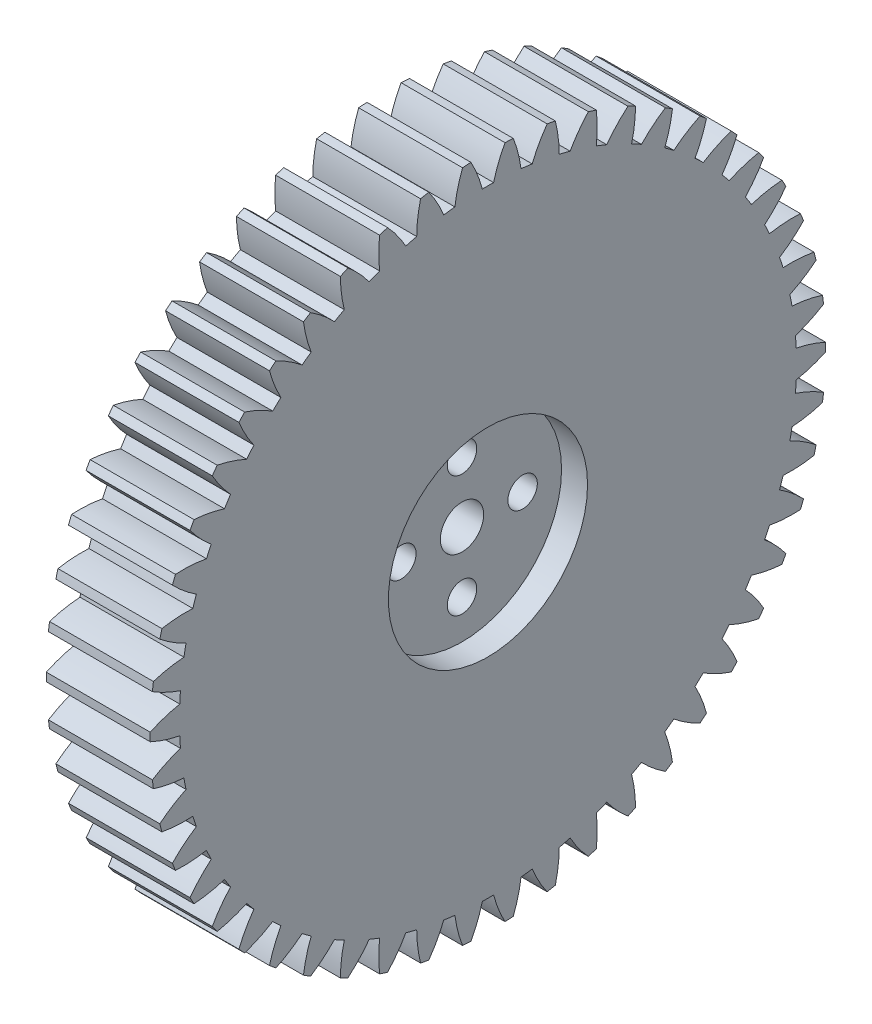
SolidWorks part; units mm, degrees
ref_plane "Plane1" through (0, 0, 0) normal (0, 0, 1) x (1, 0, 0)
ref_plane "Plane2" through (0, 0, 0) normal (0, 1, 0) x (1, 0, 0)
ref_plane "Plane3" through (0, 0, 0) normal (1, 0, 0) x (0, 0, -1)
sketch "HoldingSke" plane through (0, 0, 0) normal (0, 1, 0) x (1, 0, 0)
  line L0 (0, 0) -> (0.4285, -0.5107)
  line L1 (-15, 0) -> (100, 0) construction
  line L2 (0, 0) -> (-2.1039, 2.3779)
  line L3 (0, 0) -> (-11.863, 4.5341)
  line L4 (0, 0) -> (5.5511, 6.6156)
  line L5 (0, 0) -> (-46.8476, -17.4728)
  line L6 (0, 0) -> (-9.9476, -6.7116)
  line L7 (-2.1039, 2.3779) -> (8.6586, 51.2059)
  line L8 (-76.2, 54.61) -> (-74.8, 54.61)
  line L9 (-71.009, 38.7566) -> (-53.1078, 45.2721)
  line L10 (-76.2, 71.12) -> (104.1128, 71.12)
  line L11 (0, 0) -> (-12, 0)
  line L12 (-76.2, 101.6) -> (-76.147, 101.6)
  line L13 (24.9733, 27.94) -> (52.9518, 28.4284)
  line L14 (24.9733, 27.94) -> (24.9743, 27.94)
  line L15 (24.9733, 27.94) -> (100.4006, 29.5858)
  line L16 (-63.627, -1.5) -> (-12.827, -1.5)
  circle A0 centre (0, 0) radius 4
  circle A1 centre (0, 0) radius 35.624
  circle A2 centre (0, 0) radius 37.5
  circle A3 centre (0, 0) radius 4
  dimension "MHD" = 71.248
  dimension "Hub_dia" = 75
  dimension "Bore" = 8
  dimension "MBD" = 8
  dimension "Num_teeth" = 50
  dimension "Pitch" = 0.6667
  dimension "Overall_len" = 50
  dimension "Show_teeth" = 50
  dimension "Thickness" = 12
  dimension "OAL" = 50.0001
  dimension "T_dim" = 1.4
  dimension "Ap" = 20
  dimension "H" = 19.05
  dimension "Pitch_radius" = 180.3128
  dimension "Width" = 12
  dimension "Backlash" = 0.053
  dimension "Addendum_fac" = 1
  dimension "Dedendum_fac" = 1.25
  dimension "Clearance_fac" = 0.25
  dimension "Dedendum_add" = 0.001
  dimension "Module" = 1.5
sketch "BasProSke" plane through (0, 0, 0) normal (0, 1, 0) x (1, 0, 0)
  line L0 (-10, 0) -> (60, 0) construction
  line L1 (0, 0) -> (0, 39)
  line L2 (0, 0) -> (12, 0)
  line L3 (12, 0) -> (12, 39)
  line L4 (12, 39) -> (0, 39)
  dimension "Thickness" = 12
  dimension "Diameter" = 78
revolve "Base-Revolve" add sketch "BasProSke" angle 360 about L0
sketch "TooCutSke" plane through (0, 0, 0) normal (1, 0, 0) x (0, 0, -1)
  line L1 (0, 0) -> (0, 107) construction
  line L2 (0, 0) -> (-1.2706, 37.4785) construction
  line L3 (0, 0) -> (-4.7073, 74.8207) construction
  line L4 (-1.2706, 37.4785) -> (-2.3537, 37.4103) construction
  arc A0 (0.65, 35.6181) -> (-0.65, 35.6181) centre (0, 0) ccw
  arc A1 (1.9801, 38.9751) -> (-1.9801, 38.9751) centre (0, 0) ccw
  circle A2 centre (0, 0) radius 37.5 construction
  circle A3 centre (0, 0) radius 35.2385 construction
  arc A4 (-0.65, 35.6181) -> (-1.9801, 38.9751) centre (-15.1589, 31.8113) ccw
  arc A5 (1.9801, 38.9751) -> (0.65, 35.6181) centre (15.1589, 31.8113) ccw
  dimension "Root_dia" = 71.248
  dimension "Overcut_dia" = 78.0508
  dimension "Pitch_dia" = 75
  dimension "Base_dia" = 70.4769
  dimension "Flank_rad" = 15
  dimension "Half_ang" = 3.6
  dimension "Half_CT" = 1.0852
extrude "ToothCut" cut sketch "TooCutSke" along normal through all
fillet "Breaks" [suppressed] radius 0.03
fillet "RootFillets" [suppressed] radius 0.376
pattern_circular "TeethCuts" count 50 every 7.2 about axis through (-10, 0, 0) along (1, 0, 0) of "ToothCut", "RootFillets", "Breaks"
sketch "HubNeaOneSke" plane through (0, 0, 0) normal (-1, 0, 0) x (0, 0, 1)
  circle A0 centre (0, 0) radius 35.624
  dimension "Diameter" = 71.248
extrude "HubNearOne" [suppressed] add sketch "HubNeaOneSke" along normal blind 38.0001
sketch "HubNeaBotSke" plane through (0, 0, 0) normal (-1, 0, 0) x (0, 0, 1)
  circle A0 centre (0, 0) radius 35.624
  dimension "Diameter" = 71.248
extrude "HubNearBoth" [suppressed] add sketch "HubNeaBotSke" along normal blind 19
ref_plane "FarPln" through (12, 0, 0) normal (1, 0, 0) x (0, 0, -1)
sketch "HubFarSke" plane through (12, 0, 0) normal (1, 0, 0) x (0, 0, -1)
  circle A0 centre (0, 0) radius 35.624
  dimension "Diameter" = 71.248
extrude "HubFar" [suppressed] add sketch "HubFarSke" along normal blind 19
sketch "BorSke" plane through (0, 0, 0) normal (1, 0, 0) x (0, 0, -1)
  circle A0 centre (0, 0) radius 4
  dimension "Diameter" = 8
extrude "Bore" cut sketch "BorSke" along normal mid plane 100.0001
sketch "KeySke" plane through (0, 0, 0) normal (1, 0, 0) x (0, 0, -1)
  line L0 (-1.5, 0) -> (-1.5, 5.4)
  line L1 (-1.5, 5.4) -> (1.5, 5.4)
  line L2 (1.5, 5.4) -> (1.5, 0)
  line L3 (0, 0) -> (0, 34) construction
  line L4 (-1.5, 0) -> (1.5, 0)
  dimension "Offset" = 5.4
  dimension "Width" = 3
extrude "Keyway" [suppressed] cut sketch "KeySke" along normal mid plane 100.0001
pattern_circular "Keyway2" [suppressed] count 2 every 90 about axis through (-10, 0, 0) along (1, 0, 0)
sketch "Sketch4" plane through (12, 0, 0) normal (1, 0, 0) x (0, 0, -1)
  circle A0 centre (0, 0) radius 11.5
extrude "Cut-Extrude1" cut sketch "Sketch4" against normal blind 3
sketch "Sketch5" plane through (9, 0, 0) normal (1, 0, 0) x (0, 0, -1)
  circle A0 centre (0, 7) radius 1.7
  circle A1 centre (0, 0) radius 4 construction
  circle A2 centre (7, 0) radius 1.7
  circle A3 centre (0, -7) radius 1.7
  circle A4 centre (-7, 0) radius 1.7
  point P13 (0, 0)
  dimension "D1" = 7
  dimension "D2" = 4
extrude "Cut-Extrude2" cut sketch "Sketch5" against normal blind 12
sketch "Sketch6" plane through (0, 0, 0) normal (-1, 0, 0) x (0, 0, 1)
  circle A0 centre (0, 0) radius 4
  circle A1 centre (0, 0) radius 2.5
extrude "Boss-Extrude1" add sketch "Sketch6" against normal blind 9
sketch "Sketch7" plane through (0, 0, 0) normal (-1, 0, 0) x (0, 0, 1)
  circle A0 centre (0, 0) radius 11.25
extrude "Cut-Extrude3" cut sketch "Sketch7" against normal blind 3
equation "' \"Module@HoldingSke\" = 6.35"
equation "' \"Num_teeth@HoldingSke\" = 12"
equation "' \"Ap@HoldingSke\" =  20"
equation "' \"Ap@HoldingSke\" = 20"
equation "' \"Width@HoldingSke\" = 0.5 * 25.4"
equation "' \"Hub_dia@HoldingSke\"= 1 * 25.4"
equation "' \"Hub_dia@HoldingSke\" = 1 * 25.4"
equation "' \"Overall_len@HoldingSke\" = 1.0 * 25.4"
equation "' \"Bore@HoldingSke\" = 0.75 * 25.4"
equation "' \"T_dim@HoldingSke\" = 0.1 * 25.4"
equation "' \"Width@KeySke\" = 0.25 * 25.4"
equation "' \"Show_teeth@HoldingSke\" = 13"
equation "' \"Backlash@HoldingSke\" = 0.009 * 25.4"
equation "' \"Addendum_fac@HoldingSke\" = 1.0"
equation "' \"Dedendum_fac@HoldingSke\" = 1.25"
equation "' \"Dedendum_add@HoldingSke\" = 0.00005 * 25.4"
equation "' \"Clearance_fac@HoldingSke\" = 0.25"
equation "\"Pitch@HoldingSke\" = 1 / \"Module@HoldingSke\""
equation "\"Overcut_dia@TooCutSke\" = (\"Num_teeth@HoldingSke\" + 2 * \"Addendum_fac@HoldingSke\") / \"Pitch@HoldingSke\" + 0.002 * 25.4"
equation "\"Pitch_dia@TooCutSke\" = \"Num_teeth@HoldingSke\" / \"Pitch@HoldingSke\""
equation "\"Base_dia@TooCutSke\" = \"Num_teeth@HoldingSke\" / \"Pitch@HoldingSke\" * cos((\"Ap@HoldingSke\"  * 3.14159265 / 180))"
equation "\"Root_dia@TooCutSke\" = (\"Num_teeth@HoldingSke\" + 2) / \"Pitch@HoldingSke\" - 2 * (\"Addendum_fac@HoldingSke\" + \"Dedendum_fac@HoldingSke\") / \"Pitch@HoldingSke\" - \"Dedendum_add@HoldingSke\" * 2"
equation "\"Half_ang@TooCutSke\" = 180 / \"Num_teeth@HoldingSke\""
equation "\"Half_CT@TooCutSke\" = \"Num_teeth@HoldingSke\" / \"Pitch@HoldingSke\" * sin((3.14159265 / 2 / \"Num_teeth@HoldingSke\")) / 2 - 7 * \"Backlash@HoldingSke\" / 4"
equation "\"Flank_rad@TooCutSke\" = \"Num_teeth@HoldingSke\" / \"Pitch@HoldingSke\" / 5"
equation "\"Radius@RootFillets\" = \"Clearance_fac@HoldingSke\" / \"Pitch@HoldingSke\" + \"Dedendum_add@HoldingSke\""
equation "\"Break_rad@Breaks\" = 0.02 / \"Pitch@HoldingSke\""
equation "\"Thickness@HoldingSke\" = \"Width@HoldingSke\""
equation "\"OAL@HoldingSke\" = \"Thickness@HoldingSke\""
equation "\"MHD@HoldingSke\" = (\"Num_teeth@HoldingSke\" + 2) / \"Pitch@HoldingSke\" - 2 * (\"Addendum_fac@HoldingSke\" + \"Dedendum_fac@HoldingSke\")  / \"Pitch@HoldingSke\" - \"Dedendum_add@HoldingSke\" * 2"
equation "\"MBD@HoldingSke\" = (\"Num_teeth@HoldingSke\" + 2) / \"Pitch@HoldingSke\" - 2 * (\"Addendum_fac@HoldingSke\" + \"Dedendum_fac@HoldingSke\")  / \"Pitch@HoldingSke\" - \"Dedendum_add@HoldingSke\" * 2 - 0.002 * 25.4"
equation "\"MHD@HoldingSke\" = ((sgn( \"MHD@HoldingSke\" - \"Hub_dia@HoldingSke\" )-1)*( \"MHD@HoldingSke\" - \"Hub_dia@HoldingSke\" ))/-2+ \"Hub_dia@HoldingSke\""
equation "\"MBD@HoldingSke\" = ((sgn( \"MBD@HoldingSke\" - \"Bore@HoldingSke\" )-1)*( \"MBD@HoldingSke\" - \"Bore@HoldingSke\" ))/-2+ \"Bore@HoldingSke\""
equation "\"OAL@HoldingSke\" = ((sgn( \"OAL@HoldingSke\" - \"Overall_len@HoldingSke\" )+1)*( \"OAL@HoldingSke\" - \"Overall_len@HoldingSke\" ))/2 + \"Overall_len@HoldingSke\" + 0.000002 * 25.4"
equation "\"Num_teeth@TeethCuts\" = int( \"Show_teeth@HoldingSke\" ) + 1"
equation "\"Num_teeth@TeethCuts\" = ((sgn( \"Num_teeth@TeethCuts\" - \"Num_teeth@HoldingSke\" )-1)*( \"Num_teeth@TeethCuts\" - \"Num_teeth@HoldingSke\" ))/-2+ \"Num_teeth@HoldingSke\""
equation "\"Num_teeth@TeethCuts\" = ((sgn( \"Num_teeth@TeethCuts\" - 2.0)+1)*( \"Num_teeth@TeethCuts\" - 2.0))/2 +2.0"
equation "\"Angle@TeethCuts\" = 360.0 / \"Num_teeth@HoldingSke\""
equation "\"Diameter@BasProSke\" = (\"Num_teeth@HoldingSke\" + 2 * \"Addendum_fac@HoldingSke\") / \"Pitch@HoldingSke\""
equation "\"Thickness@BasProSke\"  = \"Thickness@HoldingSke\""
equation "' \"Fillet_rad@BasProSke\" =  \"Thickness@HoldingSke\" * 0.05"
equation "' \"Fillet_rad@BasProSke\" = \"Thickness@HoldingSke\" * 0.05"
equation "\"MHD@HoldingSke\" = ((sgn( \"MHD@HoldingSke\" - \"Root_dia@TooCutSke\" )-1)*( \"MHD@HoldingSke\" - \"Root_dia@TooCutSke\" ))/-2+ \"Root_dia@TooCutSke\""
equation "\"Diameter@HubNeaOneSke\" = \"MHD@HoldingSke\""
equation "\"Length@HubNearOne\" = \"OAL@HoldingSke\" - \"Thickness@BasProSke\""
equation "\"Diameter@HubNeaBotSke\" = \"MHD@HoldingSke\""
equation "\"Length@HubNearBoth\" = ( \"OAL@HoldingSke\" - \"Thickness@BasProSke\" ) / 2.0"
equation "\"Thickness@FarPln\" = \"Thickness@BasProSke\""
equation "\"Diameter@HubFarSke\" = \"MHD@HoldingSke\""
equation "\"Length@HubFar\" = ( \"OAL@HoldingSke\" - \"Thickness@BasProSke\" ) / 2.0"
equation "\"Diameter@BorSke\" = \"MBD@HoldingSke\""
equation "\"D1@Bore\" = \"OAL@HoldingSke\" * 2.0"
equation "\"D1@Keyway\" = \"OAL@HoldingSke\" * 2.0"
equation "\"Offset@KeySke\" = \"T_dim@HoldingSke\" + \"MBD@HoldingSke\" / 2.0"
